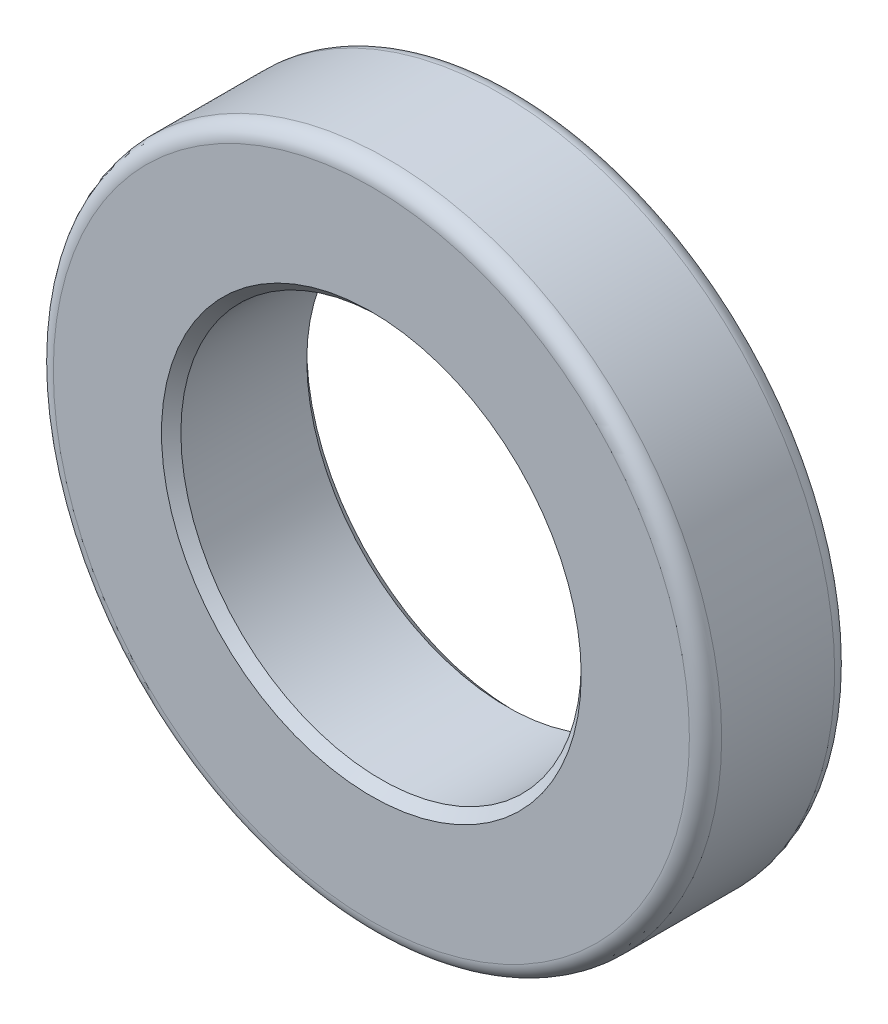
SolidWorks part; units mm, degrees
ref_plane "Front Plane" through (0, 0, 0) normal (0, 0, 1) x (1, 0, 0)
ref_plane "Top Plane" through (0, 0, 0) normal (0, 1, 0) x (1, 0, 0)
ref_plane "Right Plane" through (0, 0, 0) normal (1, 0, 0) x (0, 0, -1)
sketch "Sketch1" plane through (0, 0, 0) normal (0, 0, 1) x (1, 0, 0)
  circle A0 centre (0, 0) radius 2.6289
  circle A1 centre (0, 0) radius 1.5748
  dimension "D1" = 5.2578
  dimension "D2" = 3.1496
extrude "Boss-Extrude1" add sketch "Sketch1" along normal blind 1.143
fillet "Fillet1" radius 0.127 2 edges at (2.6289, 0, 0) (2.6289, 0, 1.143)
chamfer "Chamfer1" distance 0.0762 angle 45 2 edges at (1.5748, 0, 0) (1.5748, 0, 1.143)
